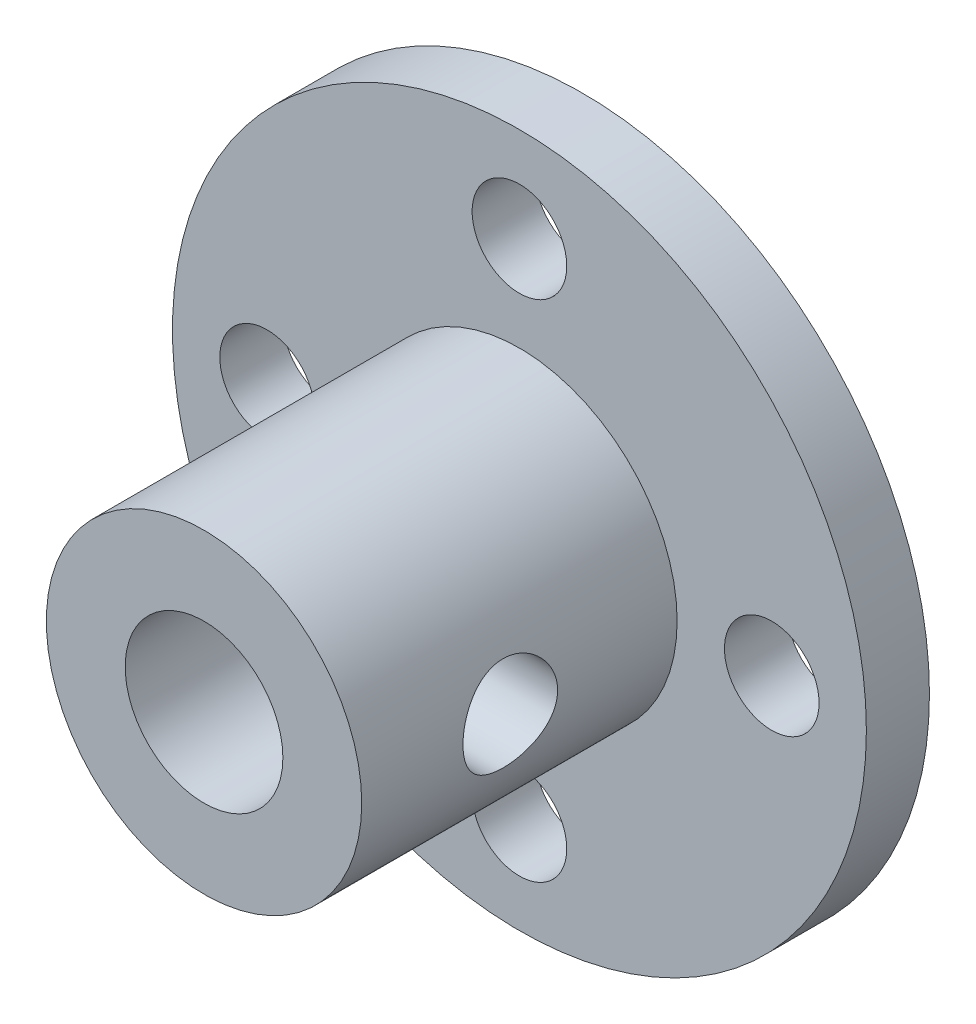
SolidWorks part; units mm, degrees
ref_plane "前视基准面" through (0, 0, 0) normal (0, 0, 1) x (1, 0, 0)
ref_plane "上视基准面" through (0, 0, 0) normal (0, 1, 0) x (1, 0, 0)
ref_plane "右视基准面" through (0, 0, 0) normal (1, 0, 0) x (0, 0, -1)
sketch "草图1" plane through (0, 0, 0) normal (0, 0, 1) x (1, 0, 0)
  circle A0 centre (0, 0) radius 11
extrude "凸台-拉伸1" add sketch "草图1" along normal blind 2
sketch "草图2" plane through (0, 0, 2) normal (0, 0, 1) x (1, 0, 0)
  circle A0 centre (0, 0) radius 5
  circle A1 centre (0, 0) radius 2.5
extrude "凸台-拉伸2" add sketch "草图2" along normal blind 10
sketch "草图3" plane through (0, 0, 2) normal (0, 0, 1) x (1, 0, 0)
  circle A0 centre (0, 0) radius 8 construction
  circle A1 centre (0, 8) radius 1.5
  circle A2 centre (8, 0) radius 1.5
  circle A3 centre (0, -8) radius 1.5
  circle A4 centre (-8, 0) radius 1.5
  point P14 (0, 0)
  dimension "D1" = 4
extrude "切除-拉伸1" cut sketch "草图3" against normal through all
sketch "草图4" plane through (0, 0, 0) normal (1, 0, 0) x (0, 0, -1)
  line L0 (-12, 0) -> (0, 0) construction
  line L1 (-12, 5) -> (-12, -5) construction
  circle A0 centre (-7.2896, 0) radius 1.5
extrude "切除-拉伸2" cut sketch "草图4" against normal through all and the other way through all
